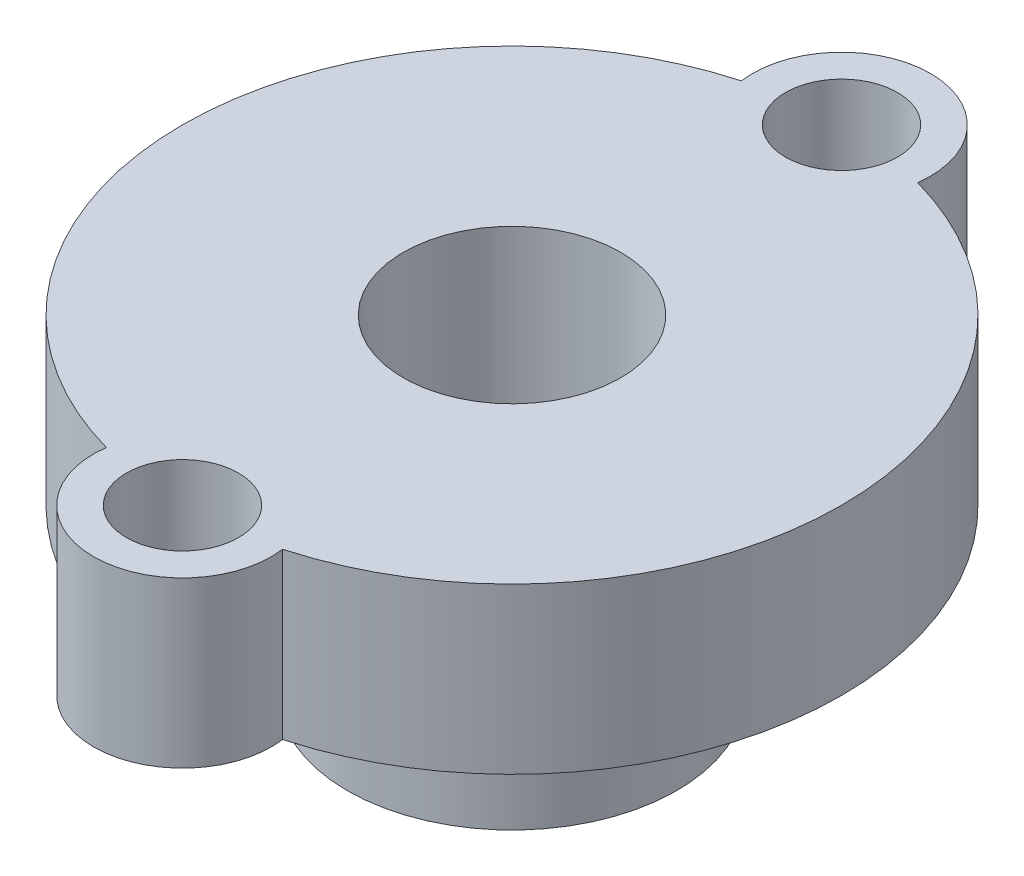
SolidWorks part; units mm, degrees
ref_plane "Alzado" through (0, 0, 0) normal (0, 0, 1) x (1, 0, 0)
ref_plane "Planta" through (0, 0, 0) normal (0, 1, 0) x (1, 0, 0)
ref_plane "Vista lateral" through (0, 0, 0) normal (1, 0, 0) x (0, 0, -1)
sketch "Croquis1" plane through (0, 0, 0) normal (0, 1, 0) x (1, 0, 0)
  circle A0 centre (0, 0) radius 5
  dimension "D1" = 10
extrude "Saliente-Extruir1" add sketch "Croquis1" along normal blind 5
sketch "Croquis2" plane through (0, 5, 0) normal (0, 1, 0) x (1, 0, 0)
  line L0 (5, 0) -> (-5, 0) construction
  arc A0 (-2.6753, 9.6355) -> (-2.6753, -9.6355) centre (0, 0) ccw
  circle A1 centre (0, 10) radius 1.7
  arc A2 (2.6753, 9.6355) -> (-2.6753, 9.6355) centre (0, 10) ccw
  circle A3 centre (0, 0) radius 5 construction
  circle A4 centre (0, 10) radius 2.7 construction
  arc A5 (2.6753, -9.6355) -> (-2.6753, -9.6355) centre (0, -10) cw
  circle A6 centre (0, -10) radius 1.7
  arc A7 (2.6753, -9.6355) -> (2.6753, 9.6355) centre (0, 0) ccw
  point P7 (2.7, 7.5)
  dimension "D1" = 20
  dimension "D2" = 3.4
  dimension "D3" = 1
extrude "Saliente-Extruir2" add sketch "Croquis2" along normal blind 5
hole_wizard "Taladro de margen para M61" positions "Croquis4" profile "Croquis6" hole size "M6" standard "ISO" end condition through all
sketch "Croquis4" plane through (0, 0, 0) normal (0, -1, 0) x (-1, 0, 0)
  point P0 (0, 0)
sketch "Croquis6" plane through (0, 0, 0) normal (1, 0, 0) x (0, 0, -1)
  line L0 (0, 0) -> (0, 10)
  line L1 (0, 10) -> (3.3, 10)
  line L2 (3.3, 10) -> (3.3, 0)
  line L5 (3.3, 0) -> (0, 0)
  line L11 (0, -6.35) -> (0, 107.95) construction
  dimension "Diámetro de taladro hasta el siguiente" = 6.6
  dimension "Profundidad de taladro hasta el siguiente" = 10
